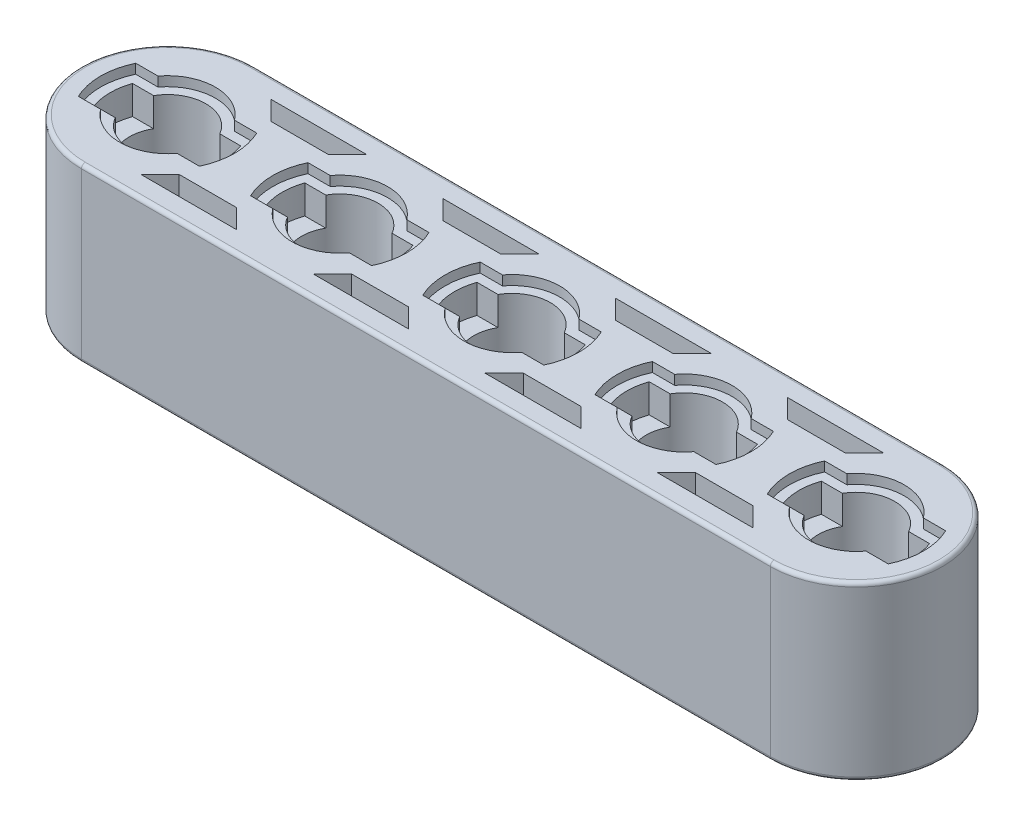
SolidWorks part; units mm, degrees
material "PBT General Purpose"
ref_plane "Front Plane" through (0, 0, 0) normal (0, 0, 1) x (1, 0, 0)
ref_plane "Top Plane" through (0, 0, 0) normal (0, 1, 0) x (1, 0, 0)
ref_plane "Right Plane" through (0, 0, 0) normal (1, 0, 0) x (0, 0, -1)
sketch "Sketch2" plane through (0, 0, 0) normal (0, 1, 0) x (1, 0, 0)
  line L0 (-18, 0) -> (18, 0) construction
  line L1 (-18, 4.5) -> (18, 4.5)
  line L2 (-18, -4.5) -> (18, -4.5)
  arc A0 (-18, 4.5) -> (-18, -4.5) centre (-18, 0) ccw
  arc A1 (18, -4.5) -> (18, 4.5) centre (18, 0) ccw
  point P2 (0, 0)
  dimension "D2" = 4.5
  dimension "Comprimento" = 36
extrude "Boss-Extrude1" add sketch "Sketch2" along normal mid plane 9
sketch "Sketch3" plane through (0, 0, 0) normal (0, 1, 0) x (1, 0, 0)
  circle A0 centre (-18, 0) radius 2
  dimension "D1" = 4
extrude "Cut-Extrude1" cut sketch "Sketch3" against normal through all both and the other way through all
sketch "Sketch4" plane through (0, 4.5, 0) normal (0, 1, 0) x (1, 0, 0)
  line L1 (-21, -1) -> (-15, -1)
  line L2 (-21, -1) -> (-21, 1)
  line L3 (-21, 1) -> (-15, 1)
  line L4 (-15, -1) -> (-15, 1)
  line L5 (-21, -1) -> (-15, 1) construction
  line L6 (-21, 1) -> (-15, -1) construction
  circle A0 centre (-18, 0) radius 3
  point P0 (-18, 0)
  circle M3 centre (-18, 0) radius 2
  dimension "D1" = 6
  dimension "D2" = 2
extrude "Cut-Extrude2" cut sketch "Sketch4" against normal blind 2 contours L3 A0 L1 M3 | L3 L1 M3 | L1 A0 L3 M3
sketch "Sketch5" plane through (0, 4.5, 0) normal (0, 1, 0) x (1, 0, 0)
  line L0 (-16.2679, -1) -> (-15.1716, -1) construction
  line L1 (-16.2679, 1) -> (-15.1716, 1) construction
  line L2 (-20.8284, -1) -> (-19.7321, -1) construction
  line L3 (-20.8284, 1) -> (-19.7321, 1) construction
  line L4 (-16.2679, -1) -> (-15.1716, -1)
  line L5 (-16.2679, 1) -> (-15.1716, 1)
  line L6 (-20.8284, -1) -> (-19.7321, -1)
  line L7 (-20.8284, 1) -> (-19.7321, 1)
  line L8 (-21.1623, 1.5) -> (-20, 1.5)
  line L9 (-16, 1.5) -> (-14.8377, 1.5)
  line L10 (-16, -1.5) -> (-14.8377, -1.5)
  line L11 (-21.1623, -1.5) -> (-20, -1.5)
  arc A0 (-15.1716, -1) -> (-15.1716, 1) centre (-18, 0) ccw construction
  arc A1 (-19.7321, -1) -> (-16.2679, -1) centre (-18, 0) ccw construction
  arc A2 (-20.8284, 1) -> (-20.8284, -1) centre (-18, 0) ccw construction
  arc A3 (-16.2679, 1) -> (-19.7321, 1) centre (-18, 0) ccw construction
  arc A4 (-15.1716, -1) -> (-15.1716, 1) centre (-18, 0) ccw
  arc A5 (-19.7321, -1) -> (-16.2679, -1) centre (-18, 0) ccw
  arc A6 (-20.8284, 1) -> (-20.8284, -1) centre (-18, 0) ccw
  arc A7 (-16.2679, 1) -> (-19.7321, 1) centre (-18, 0) ccw
  arc A8 (-16, 1.5) -> (-20, 1.5) centre (-18, 0) ccw
  arc A9 (-14.8377, -1.5) -> (-14.8377, 1.5) centre (-18, 0) ccw
  arc A10 (-20, -1.5) -> (-16, -1.5) centre (-18, 0) ccw
  arc A11 (-21.1623, 1.5) -> (-21.1623, -1.5) centre (-18, 0) ccw
  dimension "D1" = 0.5
extrude "Cut-Extrude3" cut sketch "Sketch5" against normal blind 0.5
ref_point "Point1"
sketch "Sketch7" plane through (0, 4.5, 0) normal (0, 1, 0) x (1, 0, 0)
  line L0 (18, 4.5) -> (-18, 4.5) construction
  line L1 (-16, 3.4) -> (-11, 3.4)
  line L2 (-16, 3.4) -> (-15, 2.4)
  line L3 (-15, 2.4) -> (-12, 2.4)
  line L4 (-11, 3.4) -> (-12, 2.4)
  line L5 (-4.95, 0) -> (4.95, 0) construction
  line L6 (-11, -3.4) -> (-12, -2.4)
  line L7 (-15, -2.4) -> (-12, -2.4)
  line L8 (-16, -3.4) -> (-15, -2.4)
  line L9 (-16, -3.4) -> (-11, -3.4)
  arc A0 (-16.2679, 1) -> (-19.7321, 1) centre (-18, 0) ccw construction
  point P4 (-13.5, 2.4)
  point P5 (-13.5, 3.4)
  dimension "D5" = 3
  dimension "D1" = 5
  dimension "D2" = 3
  dimension "D3" = 1.1
  dimension "D4" = 1
extrude "Cut-Extrude5" cut sketch "Sketch7" against normal blind 3
mirror "Mirror3" about plane through (0, 0, 0) normal (0, 1, 0) of "Cut-Extrude2", "Cut-Extrude3"
mirror "Mirror4" about plane through (0, 0, 0) normal (0, 1, 0) of "Cut-Extrude5"
pattern_linear "LPattern2" count 4 spacing 9 along (1, 0, 0) of "Mirror4", "Cut-Extrude5"
pattern_linear "LPattern3" count 5 spacing 9 along (1, 0, 0) of "Cut-Extrude1", "Mirror3", "Cut-Extrude2", "Cut-Extrude3"
fillet "Fillet1" radius 0.2 8 edges at (-22.5, -4.5, 0) (0, -4.5, -4.5) (22.5, -4.5, 0) (22.5, 4.5, 0) (0, 4.5, 4.5) (-22.5, 4.5, 0) (0, -4.5, 4.5) (0, 4.5, -4.5)
sketch "Sketch13" [suppressed] plane through (0, -4.5, 0) normal (0, -1, 0) x (1, 0, 0)
  point P0 (9, 0)
pattern_linear "LPattern4" [suppressed] count 3 spacing 9
pattern_circular "CirPattern1" [suppressed] count 2 over 90
sketch "Sketch9" [suppressed] plane through (0, 4.5, 0) normal (0, 1, 0) x (1, 0, 0)
  line L4 (-12, -1) -> (-6, -1)
  line L5 (-6, -1) -> (-6, 1)
  line L6 (-6, 1) -> (-12, 1)
  line L7 (-12, 1) -> (-12, -1)
  line L8 (-12, -1) -> (-6, -1)
  line L9 (-6, -1) -> (-6, 1)
  line L10 (-6, 1) -> (-12, 1)
  line L11 (-12, 1) -> (-12, -1)
  circle A1 centre (-9, 0) radius 3
  circle A2 centre (-9, 0) radius 3
  dimension "D1" = 0
  dimension "D2" = 0
sketch "Sketch8" [suppressed] plane through (0, 4.5, 0) normal (0, 1, 0) x (1, 0, 0)
  line L8 (-7, -1.5) -> (-5.8377, -1.5)
  line L9 (-5.8377, 1.5) -> (-7, 1.5)
  line L10 (-11, 1.5) -> (-12.1623, 1.5)
  line L11 (-12.1623, -1.5) -> (-11, -1.5)
  line L12 (-7, -1.5) -> (-5.8377, -1.5)
  line L13 (-5.8377, 1.5) -> (-7, 1.5)
  line L14 (-11, 1.5) -> (-12.1623, 1.5)
  line L15 (-12.1623, -1.5) -> (-11, -1.5)
  line L16 (-6.1716, 1) -> (-7.2679, 1)
  line L17 (-7.2679, -1) -> (-6.1716, -1)
  line L18 (-11.8284, -1) -> (-10.7321, -1)
  line L19 (-10.7321, 1) -> (-11.8284, 1)
  line L20 (-6.1716, 1) -> (-7.2679, 1)
  line L21 (-7.2679, -1) -> (-6.1716, -1)
  line L22 (-11.8284, -1) -> (-10.7321, -1)
  line L23 (-10.7321, 1) -> (-11.8284, 1)
  arc A8 (-5.8377, -1.5) -> (-5.8377, 1.5) centre (-9, 0) ccw
  arc A9 (-7, 1.5) -> (-11, 1.5) centre (-9, 0) ccw
  arc A10 (-12.1623, 1.5) -> (-12.1623, -1.5) centre (-9, 0) ccw
  arc A11 (-11, -1.5) -> (-7, -1.5) centre (-9, 0) ccw
  arc A12 (-5.8377, -1.5) -> (-5.8377, 1.5) centre (-9, 0) ccw
  arc A13 (-7, 1.5) -> (-11, 1.5) centre (-9, 0) ccw
  arc A14 (-12.1623, 1.5) -> (-12.1623, -1.5) centre (-9, 0) ccw
  arc A15 (-11, -1.5) -> (-7, -1.5) centre (-9, 0) ccw
  arc A16 (-7.2679, 1) -> (-10.7321, 1) centre (-9, 0) ccw
  arc A17 (-6.1716, -1) -> (-6.1716, 1) centre (-9, 0) ccw
  arc A18 (-10.7321, -1) -> (-7.2679, -1) centre (-9, 0) ccw
  arc A19 (-11.8284, 1) -> (-11.8284, -1) centre (-9, 0) ccw
  arc A20 (-7.2679, 1) -> (-10.7321, 1) centre (-9, 0) ccw
  arc A21 (-6.1716, -1) -> (-6.1716, 1) centre (-9, 0) ccw
  arc A22 (-10.7321, -1) -> (-7.2679, -1) centre (-9, 0) ccw
  arc A23 (-11.8284, 1) -> (-11.8284, -1) centre (-9, 0) ccw
  dimension "D1" = 0
  dimension "D2" = 0
sketch "Sketch11" [suppressed] plane through (0, 4.5, 0) normal (0, 1, 0) x (1, 0, 0)
  line L4 (-2, 3.4) -> (-7, 3.4)
  line L5 (-3, 2.4) -> (-2, 3.4)
  line L6 (-6, 2.4) -> (-3, 2.4)
  line L7 (-7, 3.4) -> (-6, 2.4)
  line L8 (-2, 3.4) -> (-7, 3.4)
  line L9 (-3, 2.4) -> (-2, 3.4)
  line L10 (-6, 2.4) -> (-3, 2.4)
  line L11 (-7, 3.4) -> (-6, 2.4)
  line L12 (-6, -2.4) -> (-7, -3.4)
  line L13 (-7, -3.4) -> (-2, -3.4)
  line L14 (-2, -3.4) -> (-3, -2.4)
  line L15 (-3, -2.4) -> (-6, -2.4)
  line L16 (-6, -2.4) -> (-7, -3.4)
  line L17 (-7, -3.4) -> (-2, -3.4)
  line L18 (-2, -3.4) -> (-3, -2.4)
  line L19 (-3, -2.4) -> (-6, -2.4)
  dimension "D1" = 0
  dimension "D2" = 0
extrude "Cut-Extrude6" [suppressed] cut sketch "Sketch8" against normal blind 0.5
extrude "Cut-Extrude7" [suppressed] cut sketch "Sketch9" against normal blind 2 contours L8 A2 L10
extrude "Cut-Extrude8" [suppressed] cut sketch "Sketch11" against normal up to surface (6 mm away)
sketch "Sketch14" [suppressed] plane through (0, 4.5, 0) normal (0, 1, 0) x (1, 0, 0)
  line L0 (-6.6, -3.4) -> (-5.6, -2.4)
  line L1 (-5.6, -2.4) -> (-5.6, -2) construction
  line L2 (-7, -3.4) -> (-6.6, -3.4) construction
  line L3 (-5.6, -2) -> (-7, -3.4) construction
  line L4 (-5.6, -2.4) -> (-5.6, -2)
  line L5 (-7, -3.4) -> (-6.6, -3.4)
  line L6 (-5.6, -2) -> (-7, -3.4)
extrude "Boss-Extrude2" [suppressed] add sketch "Sketch14" against normal up to surface (3 mm away)
mirror "Mirror5" [suppressed] about plane through (0, 0, 0) normal (0, 1, 0)
